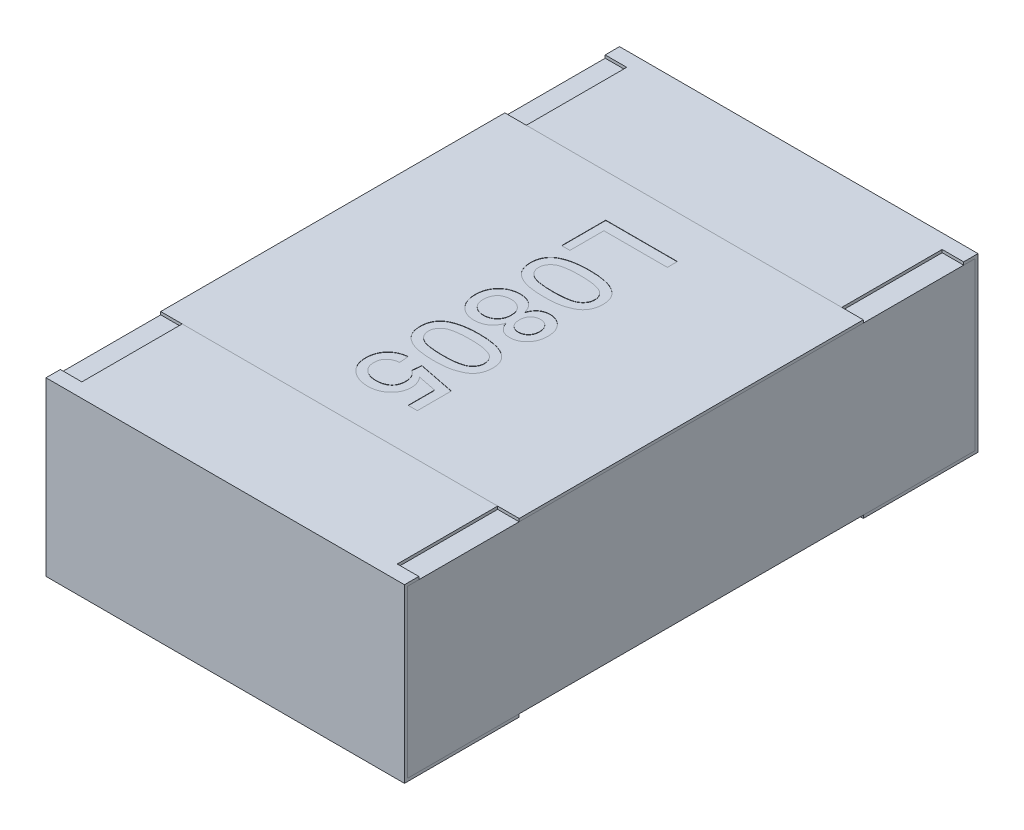
SolidWorks part; units mm, degrees
ref_plane "Front Plane" through (0, 0, 0) normal (0, 0, 1) x (1, 0, 0)
ref_plane "Top Plane" through (0, 0, 0) normal (0, 1, 0) x (1, 0, 0)
ref_plane "Right Plane" through (0, 0, 0) normal (1, 0, 0) x (0, 0, -1)
sketch "Sketch4" plane through (0, 0, 0) normal (1, 0, 0) x (0, 0, -1)
  line L0 (0, 0.1169) -> (0, -0.0721) construction
  line L1 (-1, 0) -> (0.3788, 0) construction
  line L2 (-1, 0.3) -> (-1, -0.3)
  line L3 (-1, -0.3) -> (-0.6, -0.3)
  line L4 (-0.6, 0.3) -> (-0.6, 0.29)
  line L5 (-0.6, 0.29) -> (-0.99, 0.29)
  line L6 (-0.99, 0.29) -> (-0.99, -0.29)
  line L7 (-0.99, -0.29) -> (-0.6, -0.29)
  line L8 (-0.6, -0.29) -> (-0.6, -0.3)
  line L9 (-0.6, 0.3) -> (-1, 0.3)
  line L10 (0.6, 0.3) -> (1, 0.3)
  line L11 (0.6, -0.29) -> (0.6, -0.3)
  line L12 (0.99, -0.29) -> (0.6, -0.29)
  line L13 (0.99, 0.29) -> (0.99, -0.29)
  line L14 (0.6, 0.29) -> (0.99, 0.29)
  line L15 (0.6, 0.3) -> (0.6, 0.29)
  line L16 (1, -0.3) -> (0.6, -0.3)
  line L17 (1, 0.3) -> (1, -0.3)
  dimension "LENGTH" = 1
  dimension "HEIGHT" = 0.6
  dimension "END CAP TOP LENGTH" = 0.4
  dimension "END CAP BOTTOM LENGTH" = 0.4
  dimension "D5" = 0.01
  dimension "D6" = 0.01
extrude "Boss-Extrude2" add sketch "Sketch4" along normal mid plane 1.25
sketch "Sketch5" plane through (0, 0, 0) normal (1, 0, 0) x (0, 0, -1)
  line L1 (-0.99, 0.29) -> (0.99, 0.29)
  line L2 (-0.99, 0.29) -> (-0.99, -0.29)
  line L3 (-0.99, -0.29) -> (0.99, -0.29)
  line L4 (0.99, 0.29) -> (0.99, -0.29)
extrude "Boss-Extrude3" add sketch "Sketch5" along normal up to surface and the other way up to surface separate body
sketch "Sketch6" plane through (0, 0.3, 0) normal (0, 1, 0) x (1, 0, 0)
  line L0 (-0.625, 1) -> (-0.625, 0.6) construction
  line L1 (-0.625, 0.95) -> (-0.55, 0.95)
  line L2 (-0.625, 0.95) -> (-0.625, 0.6)
  line L3 (-0.625, 0.6) -> (-0.55, 0.6)
  line L4 (-0.55, 0.95) -> (-0.55, 0.6)
  line L5 (0.625, 0.6) -> (-0.625, 0.6) construction
  line L6 (0, 0.0345) -> (0, -0.0345) construction
  line L7 (-0.0325, 0) -> (0.03, 0) construction
  line L8 (0.625, 0.95) -> (0.625, 0.6)
  line L9 (0.625, 0.6) -> (0.55, 0.6)
  line L10 (0.55, 0.95) -> (0.55, 0.6)
  line L11 (0.625, 0.95) -> (0.55, 0.95)
  line L12 (0.625, -0.95) -> (0.55, -0.95)
  line L13 (0.625, -0.95) -> (0.625, -0.6)
  line L14 (0.625, -0.6) -> (0.55, -0.6)
  line L15 (0.55, -0.95) -> (0.55, -0.6)
  line L16 (-0.625, -0.95) -> (-0.55, -0.95)
  line L17 (-0.625, -0.95) -> (-0.625, -0.6)
  line L18 (-0.625, -0.6) -> (-0.55, -0.6)
  line L19 (-0.55, -0.95) -> (-0.55, -0.6)
  dimension "TOP CUT WIDTH" = 0.075
  dimension "TOP CUT LENGTH" = 0.35
extrude "Cut-Extrude1" cut sketch "Sketch6" against normal up to surface (0.01 mm away) up to face at (0, 0.29, 0)
sketch "Sketch7" plane through (0, 0.29, 0) normal (0, 1, 0) x (1, 0, 0)
  line L1 (-0.625, 0.6) -> (0.625, 0.6)
  line L2 (-0.625, 0.6) -> (-0.625, -0.6)
  line L3 (-0.625, -0.6) -> (0.625, -0.6)
  line L4 (0.625, 0.6) -> (0.625, -0.6)
  line L5 (0.55, -0.6) -> (-0.55, -0.6) construction
  line L6 (0.55, 0.6) -> (-0.55, 0.6) construction
  line L7 (-0.625, -0.99) -> (-0.625, 0.99) construction
  line L8 (0.625, 0.99) -> (0.625, -0.99) construction
extrude "Boss-Extrude4" add sketch "Sketch7" along normal up to surface (0.01 mm away) separate body up to face at (0, 0.3, -0.875)
sketch "Sketch11" plane through (0, 0.3, 0) normal (0, 1, 0) x (1, 0, 0)
  line L0 (0, 0) -> (-0.125, 0) construction
  line L1 (-0.125, 0.515) -> (-0.125, -0.515) construction
  text T0 "L0805" font "Arial" height 0.25
  dimension "D1" = 0.125
extrude "TEXT0805" cut sketch "Sketch11" against normal blind 0.001
